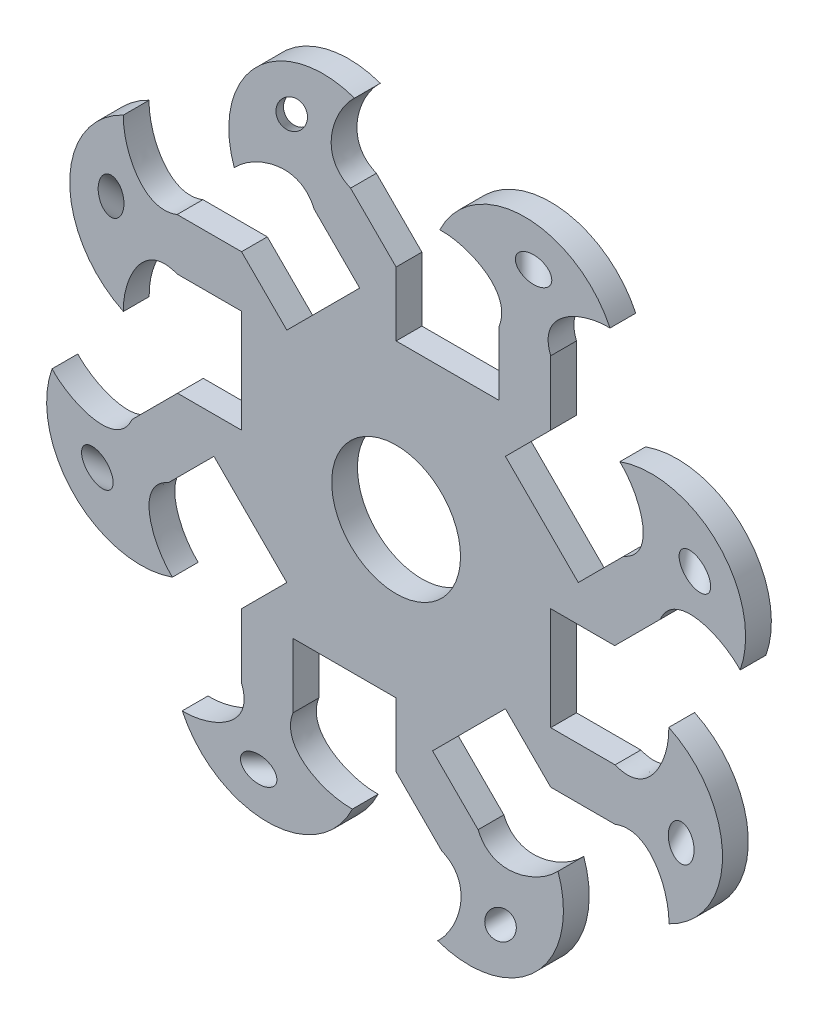
SolidWorks part; units mm, degrees
ref_plane "Front Plane" through (0, 0, 0) normal (0, 0, 1) x (1, 0, 0)
ref_plane "Top Plane" through (0, 0, 0) normal (0, 1, 0) x (1, 0, 0)
ref_plane "Right Plane" through (0, 0, 0) normal (1, 0, 0) x (0, 0, -1)
sketch "Sketch1" plane through (0, 0, 0) normal (0, 0, 1) x (1, 0, 0)
  line L1 (-6, 0) -> (-6, 4)
  line L2 (-6, 6) -> (-8.5, 6)
  line L4 (-4.2426, 4.2426) -> (-6, 6)
  line L6 (-8.5, 6) -> (-8.5, 4)
  line L8 (-8.5, 4) -> (-6, 4)
  line L10 (0, 8.4853) -> (-1.7678, 10.253)
  line L12 (-1.7678, 10.253) -> (-3.182, 8.8388)
  line L14 (-3.182, 8.8388) -> (-1.4142, 7.0711)
  line L24 (0, 6) -> (0, 8.4853)
  line L25 (-4.2426, 4.2426) -> (-1.4142, 7.0711)
  line L26 (6, 6) -> (6, 8.5)
  line L27 (6, 8.5) -> (4, 8.5)
  line L28 (4, 8.5) -> (4, 6)
  line L29 (4.2426, 4.2426) -> (6, 6)
  line L30 (0, 6) -> (4, 6)
  line L31 (8.4853, 0) -> (10.253, 1.7678)
  line L32 (10.253, 1.7678) -> (8.8388, 3.182)
  line L33 (8.8388, 3.182) -> (7.0711, 1.4142)
  line L34 (6, 0) -> (8.4853, 0)
  line L35 (4.2426, 4.2426) -> (7.0711, 1.4142)
  line L36 (6, -6) -> (8.5, -6)
  line L37 (8.5, -6) -> (8.5, -4)
  line L38 (8.5, -4) -> (6, -4)
  line L39 (4.2426, -4.2426) -> (6, -6)
  line L40 (6, 0) -> (6, -4)
  line L41 (0, -8.4853) -> (1.7678, -10.253)
  line L42 (1.7678, -10.253) -> (3.182, -8.8388)
  line L43 (3.182, -8.8388) -> (1.4142, -7.0711)
  line L44 (0, -6) -> (0, -8.4853)
  line L45 (4.2426, -4.2426) -> (1.4142, -7.0711)
  line L46 (-6, -6) -> (-6, -8.5)
  line L47 (-6, -8.5) -> (-4, -8.5)
  line L48 (-4, -8.5) -> (-4, -6)
  line L49 (-4.2426, -4.2426) -> (-6, -6)
  line L50 (0, -6) -> (-4, -6)
  line L51 (-8.4853, 0) -> (-10.253, -1.7678)
  line L52 (-10.253, -1.7678) -> (-8.8388, -3.182)
  line L53 (-8.8388, -3.182) -> (-7.0711, -1.4142)
  line L54 (-6, 0) -> (-8.4853, 0)
  line L55 (-4.2426, -4.2426) -> (-7.0711, -1.4142)
  circle A2 centre (0, 0) radius 2.5
  point P56 (0, 0)
  dimension "D3" = 8
  dimension "D2" = 5
extrude "Boss-Extrude1" add sketch "Sketch1" against normal blind 1
sketch "Sketch2" plane through (0, 0, 0) normal (0, 0, 1) x (1, 0, 0)
  line L1 (5, 8.2338) -> (5, 12.4182) construction
  line L41 (-6, 0) -> (-8.4853, 0)
  line L42 (-8.4853, 0) -> (-10.253, -1.7678)
  line L43 (-10.253, -1.7678) -> (-8.8388, -3.182)
  line L44 (-8.8388, -3.182) -> (-7.0711, -1.4142)
  line L45 (-7.0711, -1.4142) -> (-4.2426, -4.2426)
  line L46 (-4.2426, -4.2426) -> (-6, -6)
  line L47 (-6, -6) -> (-6, -8.5)
  line L48 (-6, -8.5) -> (-4, -8.5)
  line L49 (-4, -8.5) -> (-4, -6)
  line L50 (-4, -6) -> (0, -6)
  line L51 (0, -6) -> (0, -8.4853)
  line L52 (0, -8.4853) -> (1.7678, -10.253)
  line L53 (1.7678, -10.253) -> (3.182, -8.8388)
  line L54 (3.182, -8.8388) -> (1.4142, -7.0711)
  line L55 (1.4142, -7.0711) -> (4.2426, -4.2426)
  line L56 (4.2426, -4.2426) -> (6, -6)
  line L57 (6, -6) -> (8.5, -6)
  line L58 (8.5, -6) -> (8.5, -4)
  line L59 (8.5, -4) -> (6, -4)
  line L60 (6, -4) -> (6, 0)
  line L61 (6, 0) -> (8.4853, 0)
  line L62 (8.4853, 0) -> (10.253, 1.7678)
  line L63 (10.253, 1.7678) -> (8.8388, 3.182)
  line L64 (8.8388, 3.182) -> (7.0711, 1.4142)
  line L65 (7.0711, 1.4142) -> (4.2426, 4.2426)
  line L66 (4.2426, 4.2426) -> (6, 6)
  line L67 (6, 6) -> (6, 8.5)
  line L68 (6, 8.5) -> (4, 8.5)
  line L69 (4, 8.5) -> (4, 6)
  line L70 (4, 6) -> (0, 6)
  line L71 (0, 6) -> (0, 8.4853)
  line L72 (0, 8.4853) -> (-1.7678, 10.253)
  line L73 (-1.7678, 10.253) -> (-3.182, 8.8388)
  line L74 (-3.182, 8.8388) -> (-1.4142, 7.0711)
  line L75 (-1.4142, 7.0711) -> (-4.2426, 4.2426)
  line L76 (-4.2426, 4.2426) -> (-6, 6)
  line L77 (-6, 6) -> (-8.5, 6)
  line L78 (-8.5, 6) -> (-8.5, 4)
  line L79 (-8.5, 4) -> (-6, 4)
  line L80 (-6, 4) -> (-6, 0)
  line L108 (6, 8.5) -> (4, 8.5)
  arc A0 (1.6975, 10.5848) -> (8.3025, 10.5848) centre (5, 9.0125) cw
  spline S0 degree 3 poles (4, 8.5) (4.535, 9.8519) (2.7857, 10.6263) (1.6975, 10.5848) knots 0 0 0 0 1 1 1 1
  spline S1 degree 3 poles (6, 8.5) (5.465, 9.8519) (7.2143, 10.6263) (8.3025, 10.5848) knots 0 0 0 0 1 1 1 1
  dimension "D1" = 0
extrude "Boss-Extrude2" add sketch "Sketch2" against normal blind 1
sketch "Sketch3" plane through (0, 0, 0) normal (0, 0, 1) x (1, 0, 0)
  line L1 (5, 13.5855) -> (5, -8.4828) construction
  line L2 (4, 8.5) -> (4, 6) construction
  dimension "D1" = 1
ref_plane "Plane1" through (2.5, 0, -2.5) normal (0.7071, 0, -0.7071) x (0, -1, 0)
sketch "Sketch4" plane through (2.5, 0, -2.5) normal (0.7071, 0, -0.7071) x (0, -1, 0)
  line L0 (-9.8577, -1.7036) -> (-9.8577, 11.458)
  line L1 (-11.9681, 11.458) -> (0.4025, 11.458) construction
ref_plane "Plane2" through (-8.102, 0, -8.102) normal (0.7071, 0, 0.7071) x (0, -1, 0)
sketch "Sketch5" plane through (-8.102, 0, -8.102) normal (0.7071, 0, 0.7071) x (0, -1, 0)
  circle A1 centre (-11.0654, 3.7723) radius 0.5
extrude "Cut-Extrude1" cut sketch "Sketch5" against normal through all both and the other way through all contours A1
pattern_circular "CirPattern4" count 8 over 360 of "Cut-Extrude1", "Boss-Extrude2"
